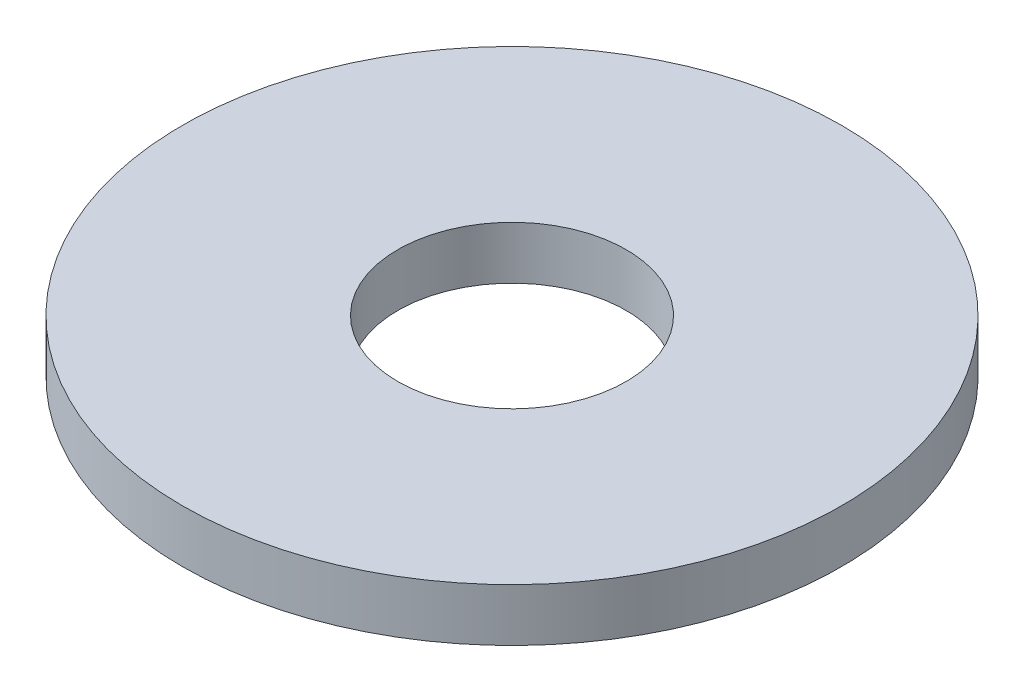
SolidWorks part; units mm, degrees
material "AISI 304"
ref_plane "前视基准面" through (0, 0, 0) normal (0, 0, 1) x (1, 0, 0)
ref_plane "上视基准面" through (0, 0, 0) normal (0, 1, 0) x (1, 0, 0)
ref_plane "右视基准面" through (0, 0, 0) normal (1, 0, 0) x (0, 0, -1)
sketch "草图1" plane through (0, 0, 0) normal (0, 1, 0) x (1, 0, 0)
  circle A0 centre (0, 0) radius 2.6
  circle A1 centre (0, 0) radius 7.5
  dimension "D1" = 5.2
  dimension "D2" = 15
extrude "凸台-拉伸1" add sketch "草图1" along normal blind 1.2
